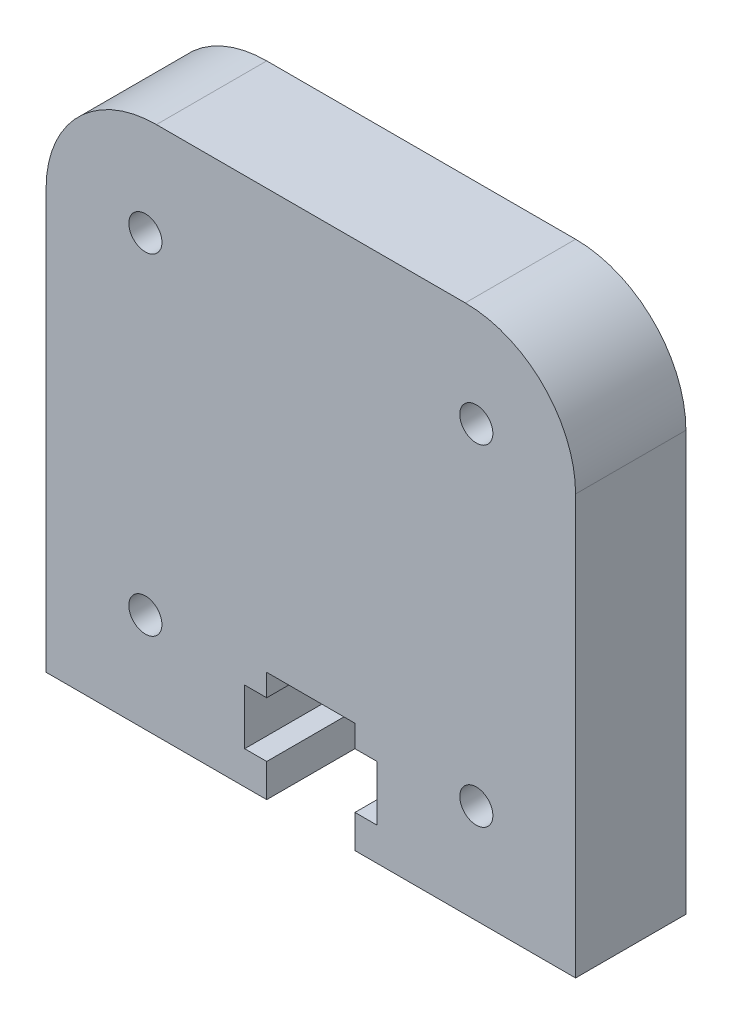
SolidWorks part; units mm, degrees
ref_plane "Front Plane" through (0, 0, 0) normal (0, 0, 1) x (1, 0, 0)
ref_plane "Top Plane" through (0, 0, 0) normal (0, 1, 0) x (1, 0, 0)
ref_plane "Right Plane" through (0, 0, 0) normal (1, 0, 0) x (0, 0, -1)
sketch "Sketch1" plane through (0, 0, 0) normal (0, 0, 1) x (1, 0, 0)
  line L1 (-7.5, 7.5) -> (7.5, 7.5) construction
  line L2 (-7.5, 7.5) -> (-7.5, -7.5) construction
  line L3 (-7.5, -7.5) -> (7.5, -7.5) construction
  line L4 (7.5, 7.5) -> (7.5, -7.5) construction
  line L5 (-7.5, 7.5) -> (7.5, -7.5) construction
  line L6 (-7.5, -7.5) -> (7.5, 7.5) construction
  line L7 (-12, 12) -> (12, 12)
  line L8 (-12, 12) -> (-12, -12)
  line L9 (-12, -12) -> (12, -12)
  line L10 (12, 12) -> (12, -12)
  line L11 (-12, 12) -> (12, -12) construction
  line L12 (-12, -12) -> (12, 12) construction
  circle A0 centre (-7.5, 7.5) radius 0.75
  circle A1 centre (7.5, 7.5) radius 0.75
  circle A2 centre (7.5, -7.5) radius 0.75
  circle A3 centre (-7.5, -7.5) radius 0.75
  point P0 (0, 0)
  point P6 (0, 0)
  dimension "D2" = 1.5
  dimension "D1" = 15
  dimension "D5" = 24
  dimension "D6" = 24
  dimension "D3" = 2
  dimension "D4" = 2
extrude "Boss-Extrude1" add sketch "Sketch1" along normal blind 5
fillet "Fillet1" radius 5 2 edges at (-12, 12, 2.5) (12, 12, 2.5)
sketch "Sketch2" plane through (0, 0, 5) normal (0, 0, 1) x (1, 0, 0)
  line L0 (0, 0) -> (0, -14.4753) construction
  line L1 (-2, -12) -> (-2, -10.5)
  line L2 (-12, -12) -> (12, -12) construction
  line L3 (-2, -10.5) -> (-3, -10.5)
  line L4 (-3, -10.5) -> (-3, -8)
  line L5 (-3, -8) -> (-2, -8)
  line L6 (-2, -8) -> (-2, -7)
  line L7 (-2, -7) -> (2, -7)
  line L8 (2, -7) -> (2, -8)
  line L9 (2, -8) -> (3, -8)
  line L10 (3, -8) -> (3, -10.5)
  line L11 (3, -10.5) -> (2, -10.5)
  line L12 (2, -10.5) -> (2, -12)
  line L13 (2, -12) -> (-2, -12)
  point P7 (0, -7)
  point P18 (0, -12)
  dimension "D1" = 4
  dimension "D2" = 1.5
  dimension "D3" = 5
  dimension "D4" = 2.5
  dimension "D5" = 1
extrude "Cut-Extrude1" cut sketch "Sketch2" against normal blind 10
